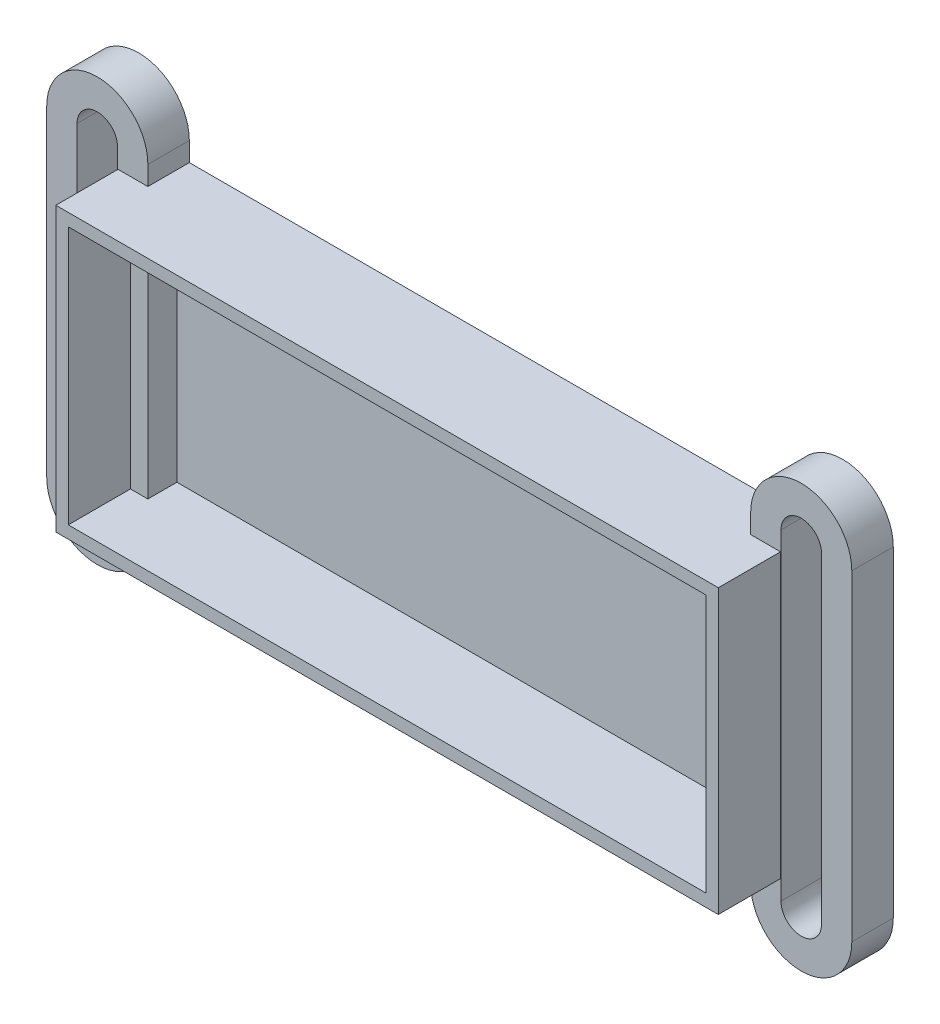
SolidWorks part; units mm, degrees
ref_plane "Front Plane" through (0, 0, 0) normal (0, 0, 1) x (1, 0, 0)
ref_plane "Top Plane" through (0, 0, 0) normal (0, 1, 0) x (1, 0, 0)
ref_plane "Right Plane" through (0, 0, 0) normal (1, 0, 0) x (0, 0, -1)
sketch3d "3DSketch1"
  line L1 (-40.4303, 18.8073, 0) -> (21.0697, 18.8073, 0)
  line L2 (-40.4303, 18.8073, 0) -> (-40.4303, -6.0927, 0)
  line L3 (-40.4303, -6.0927, 0) -> (21.0697, -6.0927, 0)
  line L4 (21.0697, 18.8073, 0) -> (21.0697, -6.0927, 0)
  line L5 (-41.6303, 20.0073, 0) -> (22.2697, 20.0073, 0)
  line L6 (-41.6303, 20.0073, 0) -> (-41.6303, -7.2927, 0)
  line L7 (-41.6303, -7.2927, 0) -> (22.2697, -7.2927, 0)
  line L8 (22.2697, 20.0073, 0) -> (22.2697, -7.2927, 0)
  dimension "D1" = 24.9
  dimension "D2" = 61.5
  dimension "D3" = 1.2
  dimension "D4" = 1.2
  dimension "D5" = 1.2
  dimension "D6" = 1.2
extrude "Boss-Extrude1" add sketch "3DSketch1" along direction (0, 0, 1) on the side of the normal blind 10
sketch "Sketch2" plane through (0, 0, 0) normal (0, 0, -1) x (-1, 0, 0)
  line L1 (-22.2697, 20.0073) -> (41.6303, 20.0073)
  line L2 (-22.2697, 20.0073) -> (-22.2697, -7.2927)
  line L3 (-22.2697, -7.2927) -> (41.6303, -7.2927)
  line L4 (41.6303, 20.0073) -> (41.6303, -7.2927)
extrude "Boss-Extrude2" add sketch "Sketch2" against normal blind 1.2
sketch "Sketch4" plane through (0, 0, 0) normal (0, 0, -1) x (-1, 0, 0)
  line L0 (-22.2697, 6.3573) -> (63.0465, 6.3573)
  line L1 (-22.2697, 20.0073) -> (41.6303, 20.0073)
  line L2 (-22.2697, 20.0073) -> (-22.2697, -7.2927)
  line L3 (-22.2697, -7.2927) -> (41.6303, -7.2927)
  line L4 (41.6303, 20.0073) -> (41.6303, -7.2927)
  line L5 (41.6303, 6.3573) -> (45.6303, 6.3573)
  line L6 (45.6303, 21.8573) -> (45.6303, -9.1427)
  line L7 (48.6303, 24.8573) -> (48.6303, -12.1427)
  line L8 (9.6803, 40.7704) -> (9.6803, -38.6507)
  line L9 (41.6303, 20.0073) -> (38.6303, 20.0073)
  line L10 (41.6303, 6.3573) -> (45.1303, 6.3573)
  line L13 (41.6303, 6.3573) -> (43.6303, 6.3573)
  line L16 (43.6303, 21.8573) -> (43.6303, -9.1427) construction
  line L17 (45.5847, 21.8573) -> (45.5847, -9.1427)
  line L18 (41.6759, 21.8573) -> (41.6759, -9.1427)
  line L19 (43.6303, 21.8573) -> (43.6303, -9.1427) construction
  line L20 (48.5075, 21.8573) -> (48.5075, -9.1427)
  line L21 (38.7531, 21.8573) -> (38.7531, -9.1427)
  line L22 (-24.2697, 21.8573) -> (-24.2697, -9.1427) construction
  line L23 (-29.1469, 21.8573) -> (-29.1469, -9.1427)
  line L24 (-19.3925, 21.8573) -> (-19.3925, -9.1427)
  line L25 (-24.2697, 21.8573) -> (-24.2697, -9.1427) construction
  line L26 (-26.2241, 21.8573) -> (-26.2241, -9.1427)
  line L27 (-22.3153, 21.8573) -> (-22.3153, -9.1427)
  arc A4 (45.5847, 21.8573) -> (41.6759, 21.8573) centre (43.6303, 21.8573) ccw
  arc A5 (41.6759, -9.1427) -> (45.5847, -9.1427) centre (43.6303, -9.1427) ccw
  arc A6 (48.5075, 21.8573) -> (38.7531, 21.8573) centre (43.6303, 21.8573) ccw
  arc A7 (38.7531, -9.1427) -> (48.5075, -9.1427) centre (43.6303, -9.1427) ccw
  arc A8 (-29.1469, 21.8573) -> (-19.3925, 21.8573) centre (-24.2697, 21.8573) cw
  arc A9 (-19.3925, -9.1427) -> (-29.1469, -9.1427) centre (-24.2697, -9.1427) cw
  arc A10 (-26.2241, 21.8573) -> (-22.3153, 21.8573) centre (-24.2697, 21.8573) cw
  arc A11 (-22.3153, -9.1427) -> (-26.2241, -9.1427) centre (-24.2697, -9.1427) cw
  point P16 (43.6303, 6.3573)
  point P26 (43.6303, 6.3573)
  point P33 (0, 0)
  point P34 (43.6303, 21.8573)
  point P35 (0, 0)
  point P36 (43.6303, -9.1427)
  point P39 (-24.2697, 6.3573)
  point P46 (-24.2697, 6.3573)
  dimension "D1" = 4
  dimension "D2" = 15.5
  dimension "D3" = 15.5
  dimension "D4" = 3
  dimension "D5" = 18.5
  dimension "D6" = 18.5
  dimension "D7" = 3
  dimension "D8" = 2
extrude "Boss-Extrude3" add sketch "Sketch4" against normal blind 4
